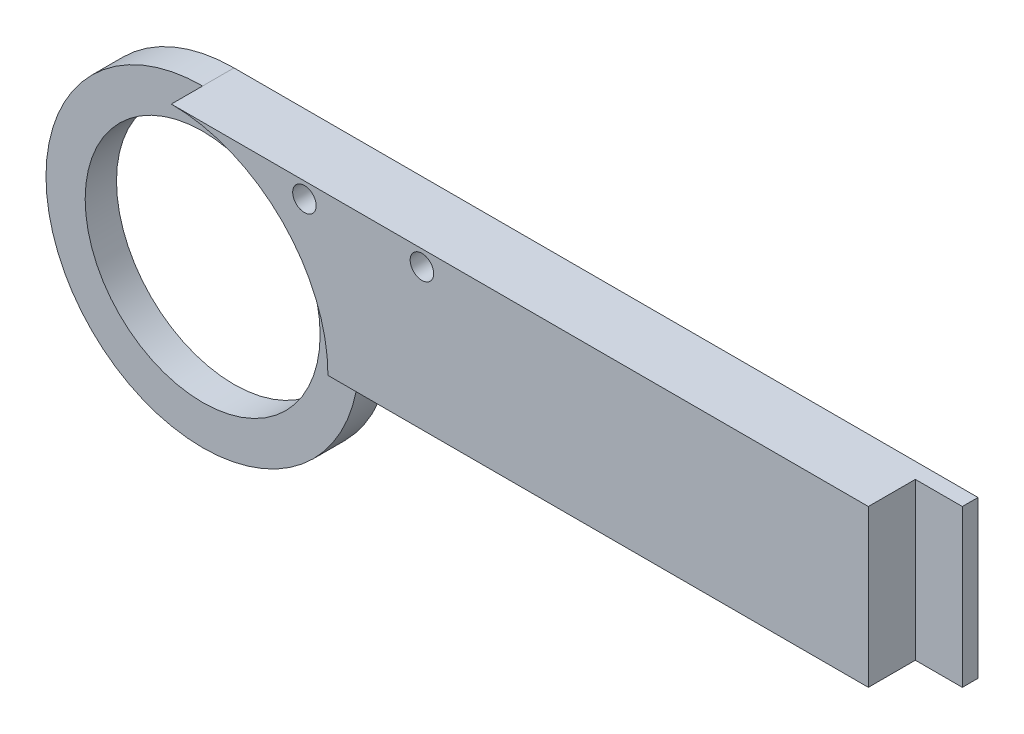
SolidWorks part; units mm, degrees
ref_plane "Plan de face" through (0, 0, 0) normal (0, 0, 1) x (1, 0, 0)
ref_plane "Plan de dessus" through (0, 0, 0) normal (0, 1, 0) x (1, 0, 0)
ref_plane "Plan de droite" through (0, 0, 0) normal (1, 0, 0) x (0, 0, -1)
sketch "Esquisse1" plane through (0, 0, 0) normal (0, 0, 1) x (1, 0, 0)
  line L1 (42.6139, 23.7864) -> (-43.2113, 23.7864)
  line L2 (42.6139, 23.7864) -> (42.6139, 3.7864)
  line L3 (42.6139, 3.7864) -> (-43.2113, 3.7864)
  line L4 (-43.2113, 23.7864) -> (-43.2113, 3.7864)
  circle A0 centre (-43.2113, 3.7864) radius 20
  circle A1 centre (-43.2113, 3.7864) radius 15
  dimension "D2" = 0
  dimension "D3" = 40
  dimension "D1" = 20
extrude "Boss.-Extru.1" add sketch "Esquisse1" along normal blind 8 contours A0 L3 L2 L1 | A1 L4 A0 L3 | A1 L3 A0 L4
sketch "Esquisse2" plane through (0, 0, 8) normal (0, 0, 1) x (1, 0, 0)
  circle A0 centre (-43.2113, 3.7864) radius 15
  circle A1 centre (-43.2113, 3.7864) radius 15 construction
  circle A2 centre (-43.2113, 3.7864) radius 20
  dimension "D1" = 30
  dimension "D2" = 0
extrude "Enlèv. mat.-Extru.1" cut sketch "Esquisse2" against normal blind 4
sketch "Esquisse3" plane through (0, 0, 8) normal (0, 0, 1) x (1, 0, 0)
  line L1 (42.6139, 23.7864) -> (51.7839, 23.7864)
  line L2 (42.6139, 23.7864) -> (42.6139, 3.7864)
  line L3 (42.6139, 3.7864) -> (51.7839, 3.7864)
  line L4 (51.7839, 23.7864) -> (51.7839, 3.7864)
  dimension "D1" = 20
  dimension "D2" = 9.17
extrude "Boss.-Extru.2" add sketch "Esquisse3" against normal blind 8
sketch "Esquisse7" plane through (0, 0, 8) normal (0, 0, 1) x (1, 0, 0)
  line L0 (51.7839, 23.7864) -> (-43.2113, 23.7864) construction
  line L1 (45.7839, 23.7864) -> (51.7839, 23.7864)
  line L2 (45.7839, 23.7864) -> (45.7839, 3.7864)
  line L3 (45.7839, 3.7864) -> (51.7839, 3.7864)
  line L4 (51.7839, 23.7864) -> (51.7839, 3.7864)
  dimension "D1" = 6
extrude "Enlèv. mat.-Extru.5" cut sketch "Esquisse7" against normal blind 6
sketch "Esquisse8" plane through (0, 0, 8) normal (0, 0, 1) x (1, 0, 0)
  line L1 (45.7839, 23.7864) -> (-43.2113, 23.7864) construction
  line L2 (51.7839, 3.7864) -> (51.7839, 23.7864) construction
  circle A0 centre (-26.2161, 21.7864) radius 1.5
  circle A1 centre (-11.2161, 21.7864) radius 1.5
  dimension "D1" = 3
  dimension "D2" = 3
  dimension "D3" = 2
  dimension "D4" = 2
  dimension "D6" = 63
  dimension "D5" = 15
extrude "Enlèv. mat.-Extru.6" cut sketch "Esquisse8" against normal blind 10 contours A0 | A1
